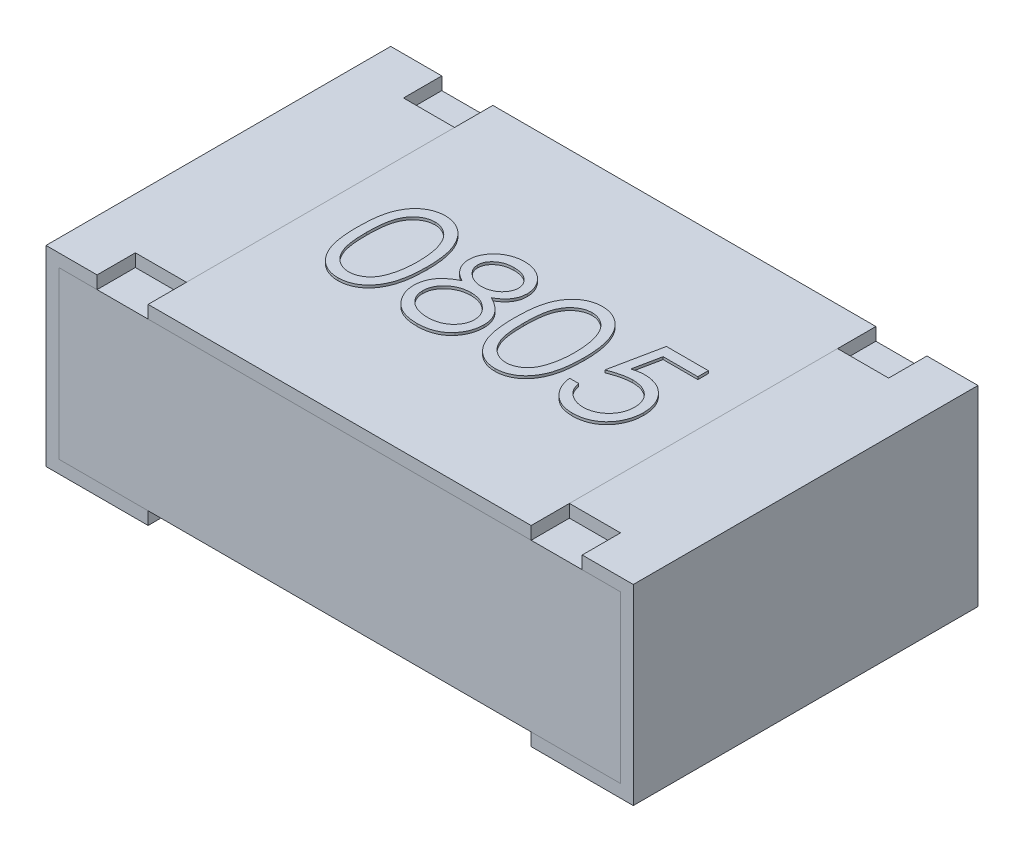
SolidWorks part; units mm, degrees
ref_plane "Front Plane" through (0, 0, 0) normal (0, 0, 1) x (1, 0, 0)
ref_plane "Top Plane" through (0, 0, 0) normal (0, 1, 0) x (1, 0, 0)
ref_plane "Right Plane" through (0, 0, 0) normal (1, 0, 0) x (0, 0, -1)
sketch "Croquis1" plane through (0, 0, 0) normal (0, 1, 0) x (1, 0, 0)
  line L1 (1.1, 0.675) -> (-1.1, 0.675)
  line L2 (1.1, 0.675) -> (1.1, -0.675)
  line L3 (1.1, -0.675) -> (-1.1, -0.675)
  line L4 (-1.1, 0.675) -> (-1.1, -0.675)
  line L5 (1.1, 0.675) -> (-1.1, -0.675) construction
  line L6 (1.1, -0.675) -> (-1.1, 0.675) construction
  point P0 (0, 0)
  dimension "D1" = 1.35
  dimension "D2" = 2.2
extrude "Extruir1" add sketch "Croquis1" along normal blind 0.7
sketch "Croquis2" plane through (0, 0, 0.675) normal (0, 0, 1) x (1, 0, 0)
  line L0 (1.1, 0.7) -> (1.1, 0) construction
  line L1 (-1.1, 0) -> (1.1, 0)
  line L2 (-1.1, 0) -> (-1.1, 0.05)
  line L3 (-1.1, 0.05) -> (1.1, 0.05)
  line L4 (1.1, 0) -> (1.1, 0.05)
  dimension "D1" = 0.05
extrude "Extruir2" cut sketch "Croquis2" against normal through all
sketch "Croquis3" plane through (0, 0, 0.675) normal (0, 0, 1) x (1, 0, 0)
  line L0 (-0.75, 0.75) -> (-1.15, 0.75)
  line L1 (-1.15, 0.75) -> (-1.15, 0)
  line L2 (-1.15, 0) -> (-0.75, 0)
  line L4 (-1.1, 0.7) -> (-1.1, 0.05) construction
  line L5 (-1.1, 0.7) -> (1.1, 0.7) construction
  dimension "D1" = 0.05
  dimension "D2" = 0.05
  dimension "D3" = 0.4
  dimension "D4" = 0.4
  dimension "D5" = 0.75
sketch3d "Croquis3D1"
  line L0 (-0.75, 0.75, 0.675) -> (-0.75, 0.75, -0.675)
  line L1 (-0.75, 0.75, -0.675) -> (-0.75, 0.7, -0.675)
  line L2 (-0.75, 0.7, -0.675) -> (-0.75, 0.7, 0.675)
  line L3 (-0.75, 0.7, 0.675) -> (-0.75, 0.75, 0.675)
  line L4 (-1.1, 0.7, -0.675) -> (-1.1, 0.7, 0.675) construction
  dimension "D1" = 0.4
sweep "Barrer1" add profiles "Croquis3D1" path "Croquis3"
ref_plane "Plano1" through (0, 0.7, 0.675) normal (1, 0, 0) x (0, 0, -1)
mirror "Simetría1" about plane through (0, 0.7, 0.675) normal (1, 0, 0) of bodies 104
sketch "Croquis4" plane through (-0.75, 0, 0) normal (1, 0, 0) x (0, 0, -1)
  line L1 (-0.675, 0.75) -> (0.675, 0.75)
  line L2 (-0.675, 0.75) -> (-0.675, 0.7)
  line L3 (-0.675, 0.7) -> (0.675, 0.7)
  line L4 (0.675, 0.75) -> (0.675, 0.7)
extrude "Extruir3" add sketch "Croquis4" along normal up to surface (1.5 mm away) separate body up to face at (0.75, 0.725, 0)
sketch "Croquis5" plane through (0, 0.75, 0) normal (0, 1, 0) x (1, 0, 0)
  line L0 (0, -0.675) -> (0, 0.675) construction
  line L1 (-0.75, -0.675) -> (-0.95, -0.675)
  line L2 (-0.75, -0.675) -> (-0.75, -0.525)
  line L3 (-0.75, -0.525) -> (-0.95, -0.525)
  line L4 (-0.95, -0.675) -> (-0.95, -0.525)
  line L5 (0.75, -0.675) -> (-0.75, -0.675) construction
  line L6 (0.75, 0.675) -> (-0.75, 0.675) construction
  line L7 (-0.75, 0) -> (0.75, 0) construction
  line L8 (-0.75, 0.675) -> (-0.75, -0.675) construction
  line L9 (0.75, 0.675) -> (0.75, -0.675) construction
  line L10 (-0.95, 0.675) -> (-0.95, 0.525)
  line L11 (-0.75, 0.525) -> (-0.95, 0.525)
  line L12 (-0.75, 0.675) -> (-0.75, 0.525)
  line L13 (-0.75, 0.675) -> (-0.95, 0.675)
  line L14 (0.75, 0.675) -> (0.95, 0.675)
  line L15 (0.75, 0.675) -> (0.75, 0.525)
  line L16 (0.75, 0.525) -> (0.95, 0.525)
  line L17 (0.95, 0.675) -> (0.95, 0.525)
  line L18 (0.95, -0.675) -> (0.95, -0.525)
  line L19 (0.75, -0.525) -> (0.95, -0.525)
  line L20 (0.75, -0.675) -> (0.75, -0.525)
  line L21 (0.75, -0.675) -> (0.95, -0.675)
  dimension "D1" = 0.15
  dimension "D2" = 0.2
extrude "Extruir4" cut sketch "Croquis5" against normal up to next (0.05 mm away)
sketch "Sketch1" plane through (0, 0.75, 0) normal (0, 1, 0) x (1, 0, 0)
  text T0 "0805" font "Century Gothic" height 0.4
extrude "Boss-Extrude1" add sketch "Sketch1" along normal blind 0.01
